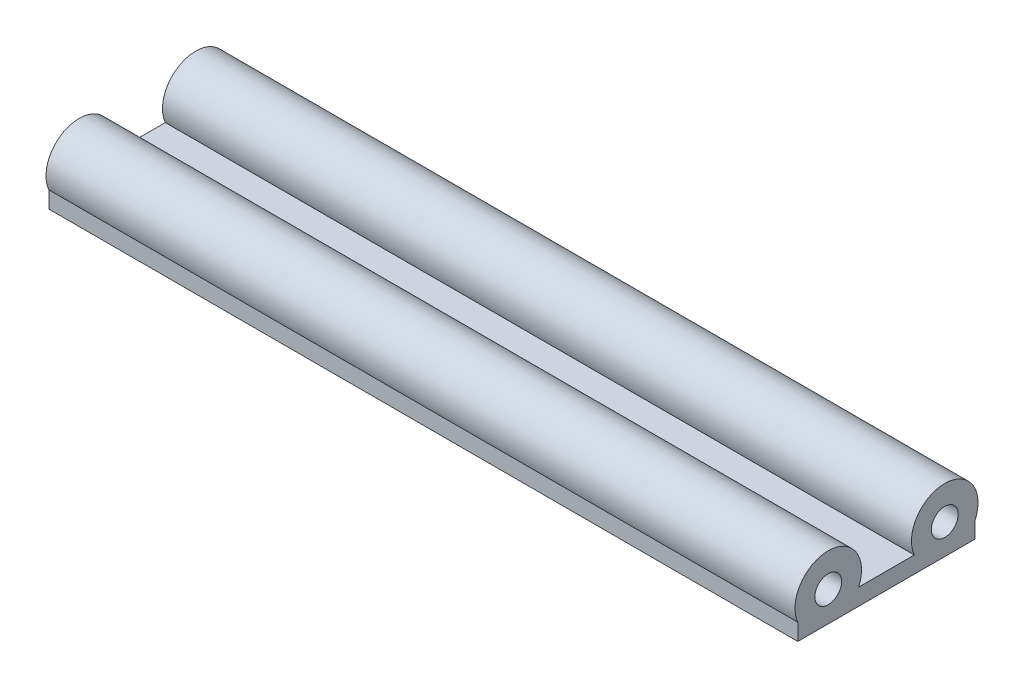
SolidWorks part; units mm, degrees
ref_plane "Front Plane" through (0, 0, 0) normal (0, 0, 1) x (1, 0, 0)
ref_plane "Top Plane" through (0, 0, 0) normal (0, 1, 0) x (1, 0, 0)
ref_plane "Right Plane" through (0, 0, 0) normal (1, 0, 0) x (0, 0, -1)
sketch "Sketch1" plane through (0, 0, 0) normal (1, 0, 0) x (0, 0, -1)
  line L4 (0, 0) -> (-28, 0) construction
  line L5 (7.3212, -3.225) -> (-72.5702, -3.225) construction
  line L6 (-20.6788, -3.225) -> (-7.3212, -3.225)
  line L7 (-35.3212, -3.225) -> (-35.3212, -7.225)
  line L8 (-35.3212, -7.225) -> (7.3212, -7.225)
  line L9 (7.3212, -7.225) -> (7.3212, -3.225)
  arc A2 (-20.6788, -3.225) -> (-35.3212, -3.225) centre (-28, 0) ccw
  arc A3 (-7.3212, -3.225) -> (7.3212, -3.225) centre (0, 0) cw
  circle A4 centre (0, 0) radius 3.225
  circle A5 centre (-28, 0) radius 3.225
  point P5 (0, 0)
  dimension "D1" = 8
  dimension "D4" = 6.45
  dimension "D5" = 8
  dimension "D2" = 6.45
  dimension "D3" = 4
  dimension "D6" = 28
extrude "Boss-Extrude1" add sketch "Sketch1" along normal blind 180
